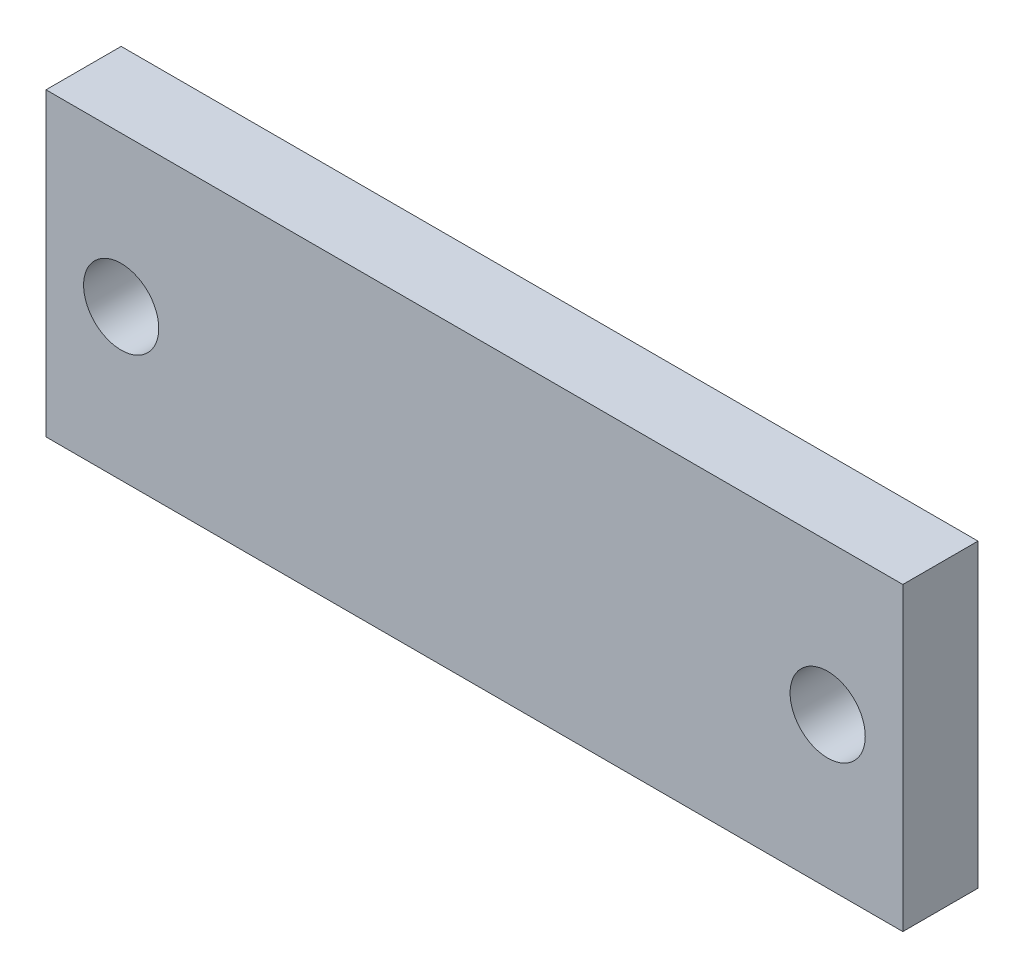
SolidWorks part; units mm, degrees
ref_plane "Front Plane" through (0, 0, 0) normal (0, 0, 1) x (1, 0, 0)
ref_plane "Top Plane" through (0, 0, 0) normal (0, 1, 0) x (1, 0, 0)
ref_plane "Right Plane" through (0, 0, 0) normal (1, 0, 0) x (0, 0, -1)
sketch "Sketch1" plane through (0, 0, 0) normal (0, 0, 1) x (1, 0, 0)
  line L0 (28.5, 0) -> (28.5, 20) construction
  line L1 (0, 0) -> (57, 0)
  line L2 (0, 0) -> (0, 20)
  line L3 (0, 20) -> (57, 20)
  line L4 (57, 0) -> (57, 20)
  line L5 (52, 10) -> (5, 10) construction
  circle A0 centre (5, 10) radius 1.75
  circle A1 centre (52, 10) radius 1.75
  circle A2 centre (5, 10) radius 2.5
  circle A3 centre (52, 10) radius 2.5
  point P11 (0, 10)
  point P12 (28.5, 10)
  dimension "D3" = 3.5
  dimension "D5" = 5
  dimension "D1" = 47
  dimension "D2" = 5
  dimension "D4" = 20
extrude "Boss-Extrude1" add sketch "Sketch1" along normal blind 5 contours L1 L4 L3 L2 A3 A2
